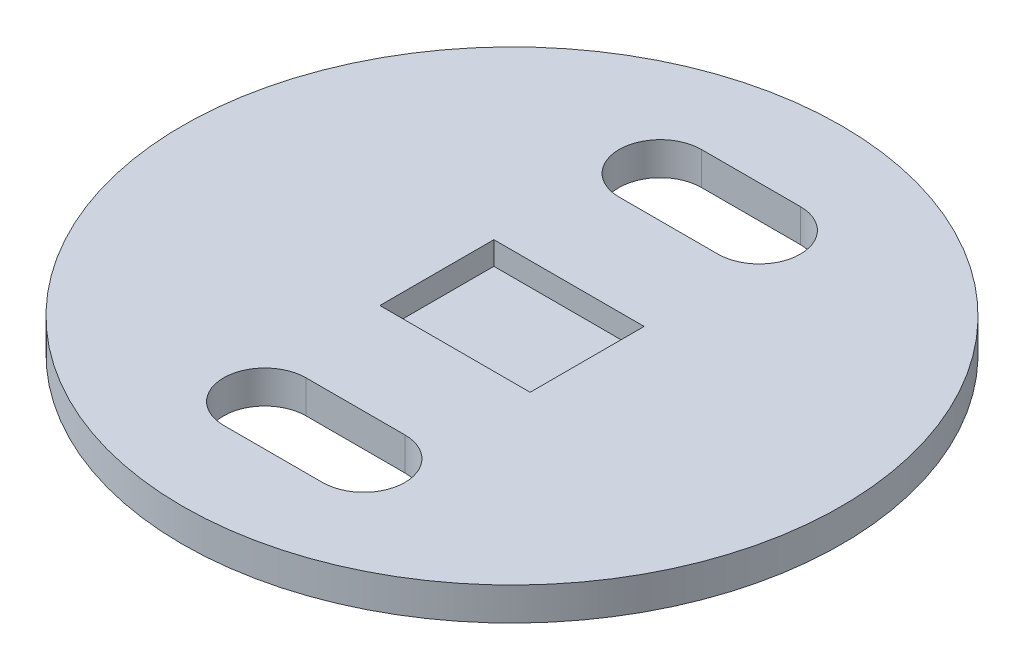
SolidWorks part; units mm, degrees
ref_plane "Front Plane" through (0, 0, 0) normal (0, 0, 1) x (1, 0, 0)
ref_plane "Top Plane" through (0, 0, 0) normal (0, 1, 0) x (1, 0, 0)
ref_plane "Right Plane" through (0, 0, 0) normal (1, 0, 0) x (0, 0, -1)
sketch "Sketch1" plane through (0, 0, 0) normal (0, 1, 0) x (1, 0, 0)
  circle A0 centre (0, 0) radius 100
  dimension "D1" = 200
extrude "Boss-Extrude1" add sketch "Sketch1" along normal blind 10
sketch "Sketch2" plane through (0, 10, 0) normal (0, 1, 0) x (1, 0, 0)
  line L0 (-15, -60) -> (15, -60) construction
  line L1 (-15, -47.5) -> (15, -47.5)
  line L2 (-15, -72.5) -> (15, -72.5)
  arc A0 (-15, -47.5) -> (-15, -72.5) centre (-15, -60) ccw
  arc A1 (15, -72.5) -> (15, -47.5) centre (15, -60) ccw
  point P2 (0, -60)
  dimension "D3" = 12.5
  dimension "D1" = 60
  dimension "D2" = 30
extrude "Cut-Extrude1" cut sketch "Sketch2" against normal through all
mirror "Mirror1" about plane through (0, 0, 0) normal (0, 0, 1) of "Cut-Extrude1"
sketch "Sketch3" plane through (0, 10, 0) normal (0, 1, 0) x (1, 0, 0)
  point P0 (0, 0)
  line B0 (-22.8, -17.3) -> (22.8, 17.3)
  line B1 (22.8, -17.3) -> (-22.8, 17.3)
  line B2 (22.8, 17.3) -> (-22.8, 17.3)
  line B3 (-22.8, 17.3) -> (-22.8, -17.3)
  line B4 (-22.8, -17.3) -> (22.8, -17.3)
  line B5 (22.8, -17.3) -> (22.8, 17.3)
sketch_block_instance "Block2-1"
sketch_block "Block2"
extrude "Cut-Extrude2" cut sketch "Sketch3" against normal blind 7 contours B1 B3 B0 | B0 B2 B1 | B1 B5 B0 | B0 B4 B1
